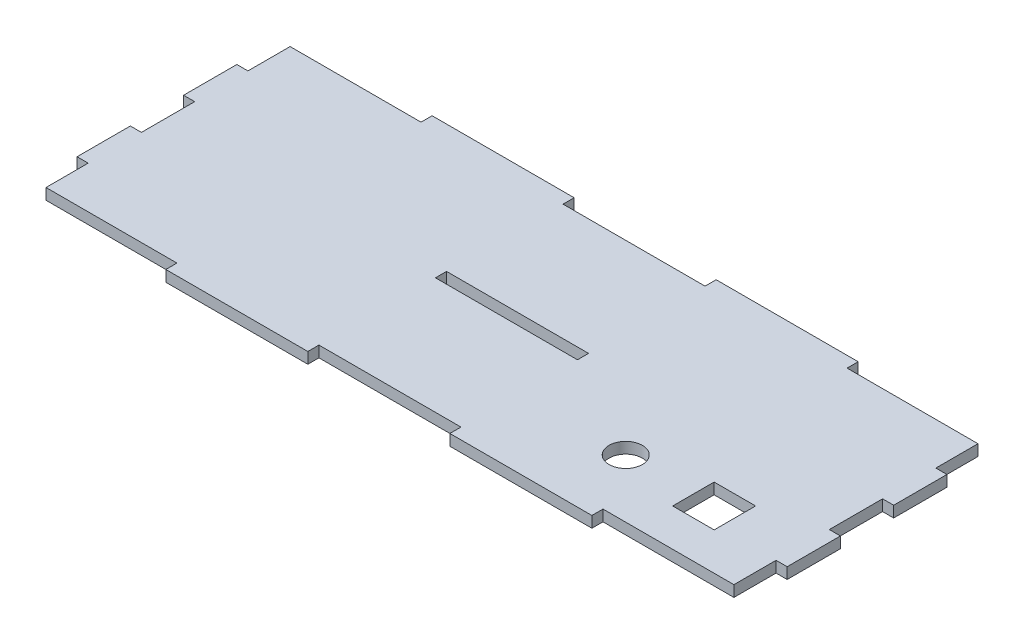
SolidWorks part; units mm, degrees
ref_plane "Front Plane" through (0, 0, 0) normal (0, 0, 1) x (1, 0, 0)
ref_plane "Top Plane" through (0, 0, 0) normal (0, 1, 0) x (1, 0, 0)
ref_plane "Right Plane" through (0, 0, 0) normal (1, 0, 0) x (0, 0, -1)
sketch "Sketch1" plane through (0, 0, 0) normal (0, 1, 0) x (1, 0, 0)
  line L1 (-101.6, -38.1) -> (101.6, -38.1)
  line L2 (-101.6, -38.1) -> (-101.6, 38.1)
  line L3 (-101.6, 38.1) -> (101.6, 38.1)
  line L4 (101.6, -38.1) -> (101.6, 38.1)
  line L5 (-101.6, -38.1) -> (101.6, 38.1) construction
  line L6 (-101.6, 38.1) -> (101.6, -38.1) construction
  point P0 (0, 0)
  dimension "D1" = 203.2
  dimension "D2" = 76.2
extrude "Boss-Extrude1" add sketch "Sketch1" along normal blind 3.175
sketch "Sketch2" plane through (0, 3.175, 0) normal (0, 1, 0) x (1, 0, 0)
  line L1 (-101.6, 38.1) -> (-60.96, 38.1)
  line L2 (-101.6, 38.1) -> (-101.6, 34.925)
  line L3 (-101.6, 34.925) -> (-60.96, 34.925)
  line L4 (-60.96, 38.1) -> (-60.96, 34.925)
  line L5 (-101.6, -38.1) -> (-60.96, -38.1)
  line L6 (-101.6, -38.1) -> (-101.6, -34.925)
  line L7 (-101.6, -34.925) -> (-60.96, -34.925)
  line L8 (-60.96, -38.1) -> (-60.96, -34.925)
  dimension "D1" = 40.64
  dimension "D2" = 3.175
  dimension "D3" = 3.175
extrude "Cut-Extrude1" cut sketch "Sketch2" against normal blind 3.175
pattern_linear "LPattern1" count 3 spacing 81.28 along (1, 0, 0) of "Cut-Extrude1"
sketch "Sketch3" plane through (0, 3.175, 0) normal (0, 1, 0) x (1, 0, 0)
  line L0 (-42.8539, 38.1) -> (80.0805, 38.1) construction
  line L2 (-56.9221, -38.1) -> (40.64, -38.1) construction
  line L3 (98.425, 38.1) -> (101.6, 38.1)
  line L4 (98.425, 38.1) -> (98.425, 22.86)
  line L5 (-101.6, 22.4009) -> (-101.6, -18.5051) construction
  line L6 (98.425, 22.86) -> (101.6, 22.86)
  line L7 (101.6, 22.8338) -> (101.6, -4.2205) construction
  line L8 (101.6, 38.1) -> (101.6, 22.86)
  line L10 (-98.425, 38.1) -> (-101.6, 38.1)
  line L11 (-98.425, 38.1) -> (-98.425, 22.86)
  line L12 (-98.425, 22.86) -> (-101.6, 22.86)
  line L13 (-101.6, 38.1) -> (-101.6, 22.86)
  dimension "D1" = 3.175
  dimension "D2" = 15.24
  dimension "D3" = 3.175
extrude "Cut-Extrude2" cut sketch "Sketch3" against normal blind 3.175
pattern_linear "LPattern2" count 3 spacing 30.48 along (0, 0, 1) of "Cut-Extrude2"
sketch "Sketch4" plane through (0, 3.175, 0) normal (0, 1, 0) x (1, 0, 0)
  line L0 (101.6, -1.5875) -> (0, -1.5875) construction
  line L1 (-101.6, -1.5875) -> (101.6, -1.5875) construction
  line L2 (-101.6, -1.5875) -> (-101.6, 1.5875) construction
  line L3 (-101.6, 1.5875) -> (101.6, 1.5875) construction
  line L4 (101.6, -1.5875) -> (101.6, 1.5875) construction
  line L5 (-101.6, -1.5875) -> (101.6, 1.5875) construction
  line L6 (-101.6, 1.5875) -> (101.6, -1.5875) construction
  line L7 (50.8, -1.5875) -> (50.8, -18.2563) construction
  line L8 (50.8, -18.2563) -> (76.0997, -18.2563) construction
  line L10 (70.1688, -24.1871) -> (82.0306, -24.1871)
  line L11 (70.1688, -24.1871) -> (70.1688, -12.3253)
  line L12 (70.1688, -12.3253) -> (82.0306, -12.3253)
  line L13 (82.0306, -24.1871) -> (82.0306, -12.3253)
  line L14 (70.1688, -24.1871) -> (82.0306, -12.3253) construction
  line L15 (70.1688, -12.3253) -> (82.0306, -24.1871) construction
  circle A0 centre (50.8, -18.2563) radius 4.7625
  point P0 (0, 0)
  dimension "D3" = 9.525
  dimension "D1" = 3.175
  dimension "D2" = 203.2
  dimension "D4" = 11.8618
  dimension "D5" = 11.8618
extrude "Cut-Extrude5" cut sketch "Sketch4" against normal blind 3.175 contours L11 L10 L13 L12 | A0
sketch "Sketch5" plane through (0, 3.175, 0) normal (0, 1, 0) x (1, 0, 0)
  line L1 (-20.32, -1.5875) -> (20.32, -1.5875)
  line L2 (-20.32, -1.5875) -> (-20.32, 1.5875)
  line L3 (-20.32, 1.5875) -> (20.32, 1.5875)
  line L4 (20.32, -1.5875) -> (20.32, 1.5875)
  line L5 (-20.32, -1.5875) -> (20.32, 1.5875) construction
  line L6 (-20.32, 1.5875) -> (20.32, -1.5875) construction
  point P0 (0, 0)
  dimension "D1" = 40.64
  dimension "D2" = 3.175
extrude "Cut-Extrude6" cut sketch "Sketch5" against normal blind 3.175
